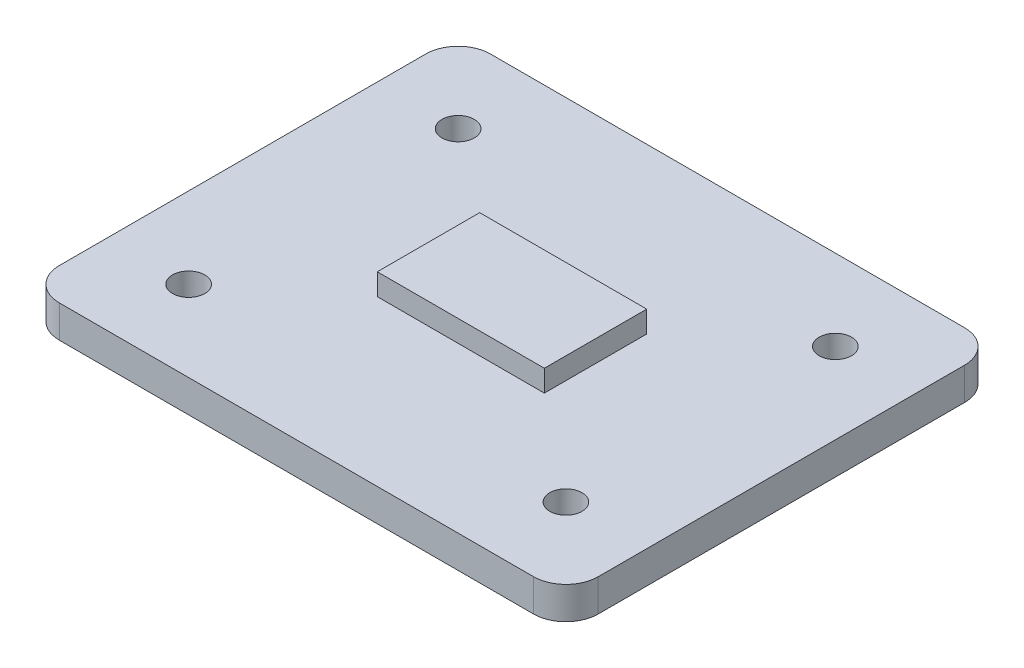
SolidWorks part; units mm, degrees
other "Bottom_body"
ref_plane "Front Plane" through (0, 0, 0) normal (0, 0, 1) x (1, 0, 0)
ref_plane "Top Plane" through (0, 0, 0) normal (0, 1, 0) x (1, 0, 0)
ref_plane "Right Plane" through (0, 0, 0) normal (1, 0, 0) x (0, 0, -1)
sketch "Sketch1" plane through (0, 0, 0) normal (0, 1, 0) x (1, 0, 0)
  line L1 (25, -20) -> (-25, -20)
  line L2 (25, -20) -> (25, 20)
  line L3 (25, 20) -> (-25, 20)
  line L4 (-25, -20) -> (-25, 20)
  line L5 (25, -20) -> (-25, 20) construction
  line L6 (25, 20) -> (-25, -20) construction
  point P0 (0, 0)
  dimension "D1" = 50
  dimension "D2" = 40
extrude "Body" add sketch "Sketch1" along normal blind 3
fillet "Fillet_Body" radius 3 4 edges at (-25, 1.5, 20) (-25, 1.5, -20) (25, 1.5, -20) (25, 1.5, 20)
sketch "Sketch2" plane through (0, 3, 0) normal (0, 1, 0) x (1, 0, 0)
  line L0 (22, 20) -> (-22, 20) construction
  line L1 (-25, 17) -> (-25, -17) construction
  line L2 (0, 25.3102) -> (0, -28.1992) construction
  line L3 (-32.0353, 0) -> (31.1369, 0) construction
  line L4 (-1.65, 0) -> (1.65, 0) construction
  circle A0 centre (-17.5, 12.5) radius 1.5
  circle A1 centre (17.5, 12.5) radius 1.5
  circle A2 centre (17.5, -12.5) radius 1.5
  circle A3 centre (-17.5, -12.5) radius 1.5
  dimension "D3" = 3
  dimension "D1" = 7.5
  dimension "D2" = 7.5
extrude "Bolts" cut sketch "Sketch2" against normal blind 9
sketch "Sketch3" plane through (0, 3, 0) normal (0, 1, 0) x (1, 0, 0)
  line L1 (7.75, -4.75) -> (-7.75, -4.75)
  line L2 (7.75, -4.75) -> (7.75, 4.75)
  line L3 (7.75, 4.75) -> (-7.75, 4.75)
  line L4 (-7.75, -4.75) -> (-7.75, 4.75)
  line L5 (7.75, -4.75) -> (-7.75, 4.75) construction
  line L6 (7.75, 4.75) -> (-7.75, -4.75) construction
  point P0 (0, 0)
  dimension "D1" = 15.5
  dimension "D2" = 9.5
extrude "Channel" add sketch "Sketch3" along normal blind 2
